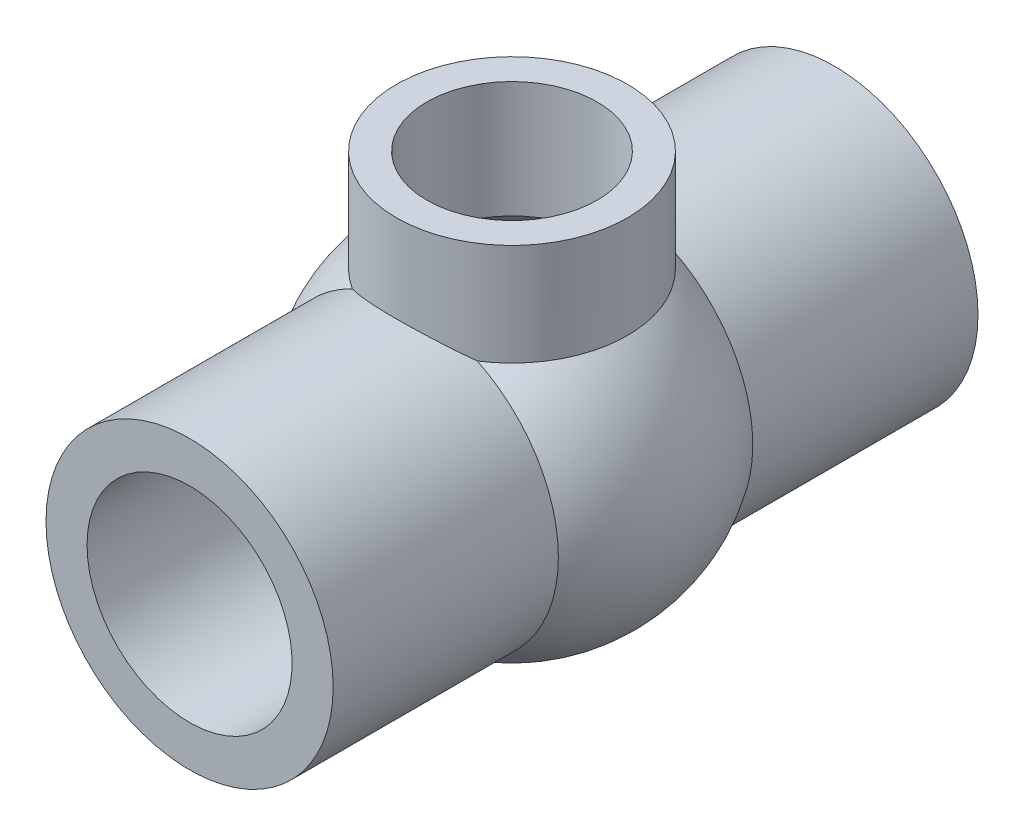
SolidWorks part; units mm, degrees
material "PVC Rigid"
ref_plane "Front Plane" through (0, 0, 0) normal (0, 0, 1) x (1, 0, 0)
ref_plane "Top Plane" through (0, 0, 0) normal (0, 1, 0) x (1, 0, 0)
ref_plane "Right Plane" through (0, 0, 0) normal (1, 0, 0) x (0, 0, -1)
sketch "Sketch1" plane through (0, 0, 0) normal (1, 0, 0) x (0, 0, -1)
  line L0 (-99.6813, 0) -> (113.9685, 0) construction
  line L1 (0, 87.2623) -> (0, -54.7313) construction
  line L2 (53, 23.6) -> (53, -21.9804)
  line L3 (53, 23.6) -> (-113.3919, 23.6)
  line L4 (53, 16.85) -> (25, 16.85)
  line L5 (25, 16.85) -> (25, 12.5)
  line L6 (25, 12.5) -> (-55.2286, 12.5)
  line L7 (19, 38) -> (19, 19.7824)
  line L8 (19, 38) -> (-12.8716, 38)
  line L9 (14, 48.357) -> (14, 34.5093)
  line L10 (-28.2449, 68) -> (14.9062, 68)
  line L11 (14.9062, 68) -> (18, 44.5)
  line L12 (18, 44.5) -> (-21.8705, 44.5)
  line L13 (50, 42.5) -> (47.0127, 65.191)
  line L14 (47.0127, 65.191) -> (14.9062, 68)
  line L15 (50, 42.5) -> (8.7303, 42.5)
  circle A0 centre (0, 0) radius 28.5
  dimension "D2" = 57
  dimension "D1" = 106
  dimension "D3" = 33.7
  dimension "D4" = 47.2
  dimension "D5" = 28
  dimension "D6" = 25
  dimension "D7" = 38
  dimension "D8" = 28
  dimension "D9" = 38
  dimension "D10" = 68
  dimension "D11" = 6.5
  dimension "D12" = 36
  dimension "D13" = 7.5
  dimension "D14" = 5
  dimension "D15" = 100
  dimension "D16" = 4.5
sketch "Sketch2" plane through (0, 0, 0) normal (1, 0, 0) x (0, 0, -1)
  line L0 (53, 23.6) -> (-113.3919, 23.6) construction
  line L2 (53, 23.6) -> (53, -21.9804) construction
  line L5 (53, 23.6) -> (15.9778, 23.6)
  line L6 (0, 53.5195) -> (0, -44.8663) construction
  line L7 (53, 23.6) -> (53, 0)
  line L8 (0, 87.2623) -> (0, -54.7313) construction
  line L9 (-53, 23.6) -> (-53, 0)
  line L10 (-97.7129, 0) -> (84.3366, 0) construction
  line L11 (-99.6813, 0) -> (113.9685, 0) construction
  line L12 (-15.9778, 23.6) -> (-53, 23.6)
  line L13 (-53, 0) -> (53, 0)
  circle A0 centre (0, 0) radius 28.5 construction
  arc A1 (15.9778, 23.6) -> (-15.9778, 23.6) centre (0, 0) ccw
revolve "RevolveBody" add sketch "Sketch2" angle 360 about L10
sketch "Sketch3" plane through (0, 0, 0) normal (1, 0, 0) x (0, 0, -1)
  line L0 (0, 61.7574) -> (0, -45.7119) construction
  line L1 (0, 87.2623) -> (0, -54.7313) construction
  line L2 (19, 38) -> (19, 19.7824) construction
  line L3 (19, 38) -> (-12.8716, 38) construction
  line L4 (19, 38) -> (19, 21.2426)
  line L5 (19, 38) -> (0, 38)
  line L6 (0, 38) -> (0, 28.5)
  circle A0 centre (0, 0) radius 28.5 construction
  arc A1 (19, 21.2426) -> (0, 28.5) centre (0, 0) ccw
revolve "RevStem" add sketch "Sketch3" angle 360 about L6
sketch "Sketch4" plane through (0, 0, 0) normal (1, 0, 0) x (0, 0, -1)
  line L1 (-66.5908, 0) -> (84.5033, 0) construction
  line L2 (53, 23.6) -> (53, -21.9804) construction
  line L3 (53, 16.85) -> (25, 16.85) construction
  line L4 (25, 16.85) -> (25, 12.5) construction
  line L5 (25, 12.5) -> (-55.2286, 12.5) construction
  line L6 (53, 16.85) -> (53, 0)
  line L7 (53, 16.85) -> (25, 16.85)
  line L8 (25, 16.85) -> (25, 12.5)
  line L9 (25, 12.5) -> (-25, 12.5)
  line L10 (0, 40.4261) -> (0, -38.2284) construction
  line L11 (0, 87.2623) -> (0, -54.7313) construction
  line L12 (-53, 16.85) -> (-53, 0)
  line L13 (-53, 16.85) -> (-25, 16.85)
  line L14 (-25, 16.85) -> (-25, 12.5)
  line L15 (53, 0) -> (-53, 0)
revolve "CoreBody" cut sketch "Sketch4" angle 360 about L15
sketch "Sketch5" plane through (0, 0, 0) normal (1, 0, 0) x (0, 0, -1)
  line L0 (0, 58.2035) -> (0, -43.7319) construction
  line L1 (0, 87.2623) -> (0, -54.7313) construction
  line L2 (19, 38) -> (-12.8716, 38) construction
  line L3 (14, 48.357) -> (14, 34.5093) construction
  line L4 (14, 38) -> (0, 38)
  line L5 (14, 38) -> (14, 18.8746)
  line L6 (0, 38) -> (0, -23.5)
  arc A0 (0, -23.5) -> (14, 18.8746) centre (0, 0) ccw
  circle A1 centre (0, 0) radius 28.5 construction
  dimension "D1" = 5
revolve "CoreStem" cut sketch "Sketch5" angle 360 about L0
scale "Scale1" bodies to scale 109 scale about centroid uniform scaling yes scale factor 0.623
